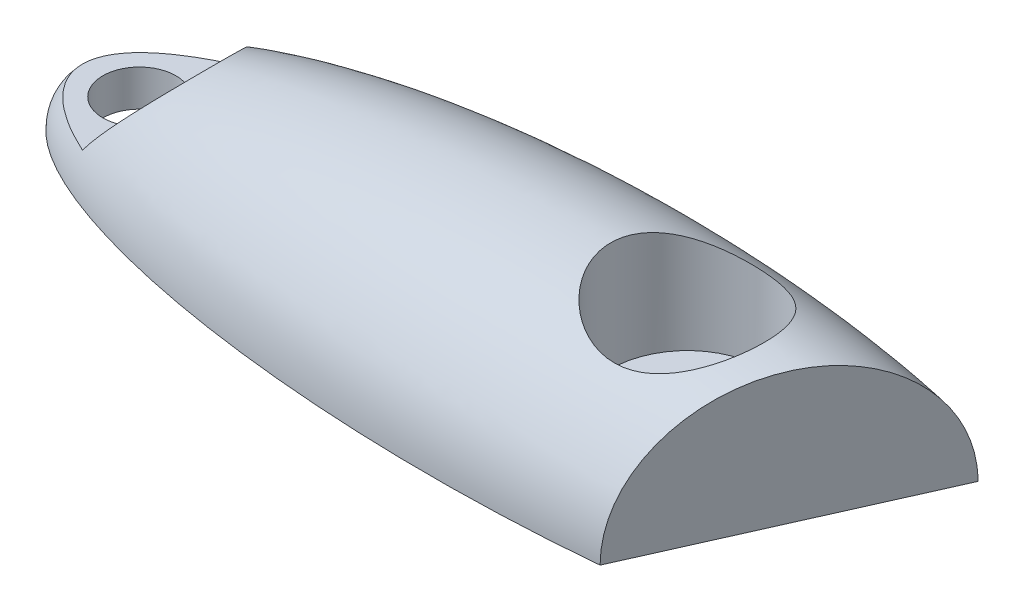
SolidWorks part; units mm, degrees
ref_plane "Front Plane" through (0, 0, 0) normal (0, 0, 1) x (1, 0, 0)
ref_plane "Top Plane" through (0, 0, 0) normal (0, 1, 0) x (1, 0, 0)
ref_plane "Right Plane" through (0, 0, 0) normal (1, 0, 0) x (0, 0, -1)
sketch "Sketch1" plane through (0, 0, 0) normal (0, 0, 1) x (1, 0, 0)
  line L0 (-14, 0) -> (14, 0) construction
  line L1 (-14, 0) -> (14, 0)
  circle A0 centre (-10.75, 0) radius 1 construction
  circle A1 centre (10.75, 0) radius 1 construction
  ellipse E0 centre (0, 0) end of major axis (14, 0) minor radius 4 (14, 0) -> (-14, 0) ccw
  dimension "D3" = 2
  dimension "D1" = 14
  dimension "D2" = 4
  dimension "D4" = 3.25
  dimension "D5" = 3.25
revolve "Revolve1" add sketch "Sketch1" angle 360 about L0
sketch "Sketch2" plane through (0, 0, 0) normal (0, 0, 1) x (1, 0, 0)
  line L1 (-26.9158, 0) -> (23.719, 0)
  line L2 (-26.9158, 0) -> (-26.9158, -13.0728)
  line L3 (-26.9158, -13.0728) -> (23.719, -13.0728)
  line L4 (23.719, 0) -> (23.719, -13.0728)
extrude "Cut-Extrude1" cut sketch "Sketch2" against normal through all both and the other way through all
sketch "Sketch3" plane through (0, 0, 0) normal (0, -1, 0) x (1, 0, 0)
  line L0 (-14, 0) -> (14, 0) construction
  circle A0 centre (-12, 0) radius 1
  circle A1 centre (3, 0) radius 1
  ellipse E0 centre (0, 0) end of major axis (14, 0) minor radius 4 (-14, 0) -> (14, 0) ccw construction
  ellipse E1 centre (0, 0) end of major axis (14, 0) minor radius 4 (14, 0) -> (-14, 0) ccw construction
  dimension "D1" = 2
  dimension "D2" = 2
  dimension "D3" = 15
extrude "Cut-Extrude2" cut sketch "Sketch3" against normal through all
ref_plane "Plane1" through (0, 1, 0) normal (0, -1, 0) x (-1, 0, 0)
sketch "Sketch4" plane through (0, 1, 0) normal (0, -1, 0) x (-1, 0, 0)
  circle A0 centre (12, 0) radius 2.1
  circle A1 centre (-3, 0) radius 2.1
  dimension "D1" = 4.2
extrude "Cut-Extrude3" cut sketch "Sketch4" against normal through all
sketch "Sketch6" plane through (0, 0, 0) normal (0, -1, 0) x (1, 0, 0)
  line L0 (-14, 0) -> (14, 0) construction
  line L3 (4.4067, 3.7967) -> (7.5933, -3.3605)
  ellipse E0 centre (0, 0) end of major axis (14, 0) minor radius 4 (14, 0) -> (-14, 0) ccw construction
  ellipse E1 centre (0, 0) end of major axis (14, 0) minor radius 4 (-14, 0) -> (14, 0) ccw construction
  ellipse E2 centre (0, 0) end of major axis (14, 0) minor radius 4 (14, 0) -> (4.4067, 3.7967) ccw
  ellipse E3 centre (0, 0) end of major axis (14, 0) minor radius 4 (7.5933, -3.3605) -> (14, 0) ccw
  point P9 (3.4169, 4)
  point P16 (7.1208, -3.4439)
  point P18 (5.1929, 4)
  point P26 (6, 0.2181)
  ellipse M7 centre (0, 0) end of major axis (14, 0) minor radius 4 (14, 0) -> (-14, 0) ccw
  ellipse M8 centre (0, 0) end of major axis (14, 0) minor radius 4 (-14, 0) -> (14, 0) ccw
  dimension "D1" = 66
  dimension "D2" = 8
extrude "Cut-Extrude5" cut sketch "Sketch6" against normal through all contours L3 L0 M7 | L0 L3 M8
